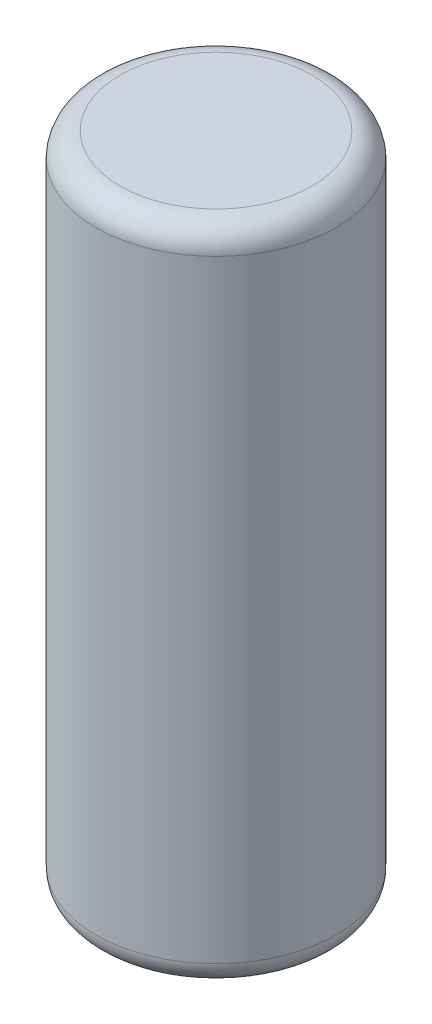
SolidWorks part; units mm, degrees
ref_plane "Front Plane" through (0, 0, 0) normal (0, 0, 1) x (1, 0, 0)
ref_plane "Top Plane" through (0, 0, 0) normal (0, 1, 0) x (1, 0, 0)
ref_plane "Right Plane" through (0, 0, 0) normal (1, 0, 0) x (0, 0, -1)
sketch "Sketch1" plane through (0, 0, 0) normal (0, 1, 0) x (1, 0, 0)
  circle A0 centre (0, 0) radius 50
  dimension "D1" = 100
extrude "Boss-Extrude1" add sketch "Sketch1" along normal blind 275
fillet "Fillet1" radius 10 2 edges at (0, 275, 50) (0, 0, 50)
